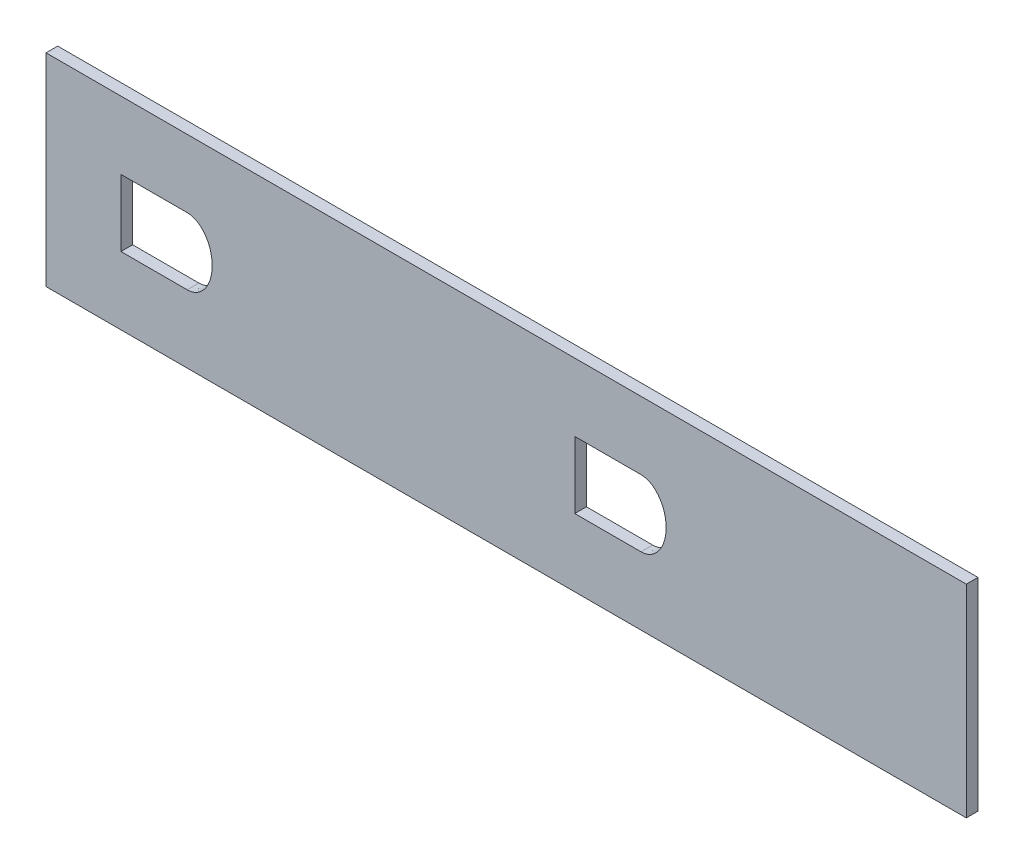
SolidWorks part; units mm, degrees
material "FiberBoard"
ref_plane "Front Plane" through (0, 0, 0) normal (0, 0, 1) x (1, 0, 0)
ref_plane "Top Plane" through (0, 0, 0) normal (0, 1, 0) x (1, 0, 0)
ref_plane "Right Plane" through (0, 0, 0) normal (1, 0, 0) x (0, 0, -1)
sketch "Sketch1" plane through (0, 0, 0) normal (0, 0, 1) x (1, 0, 0)
  line L0 (148.1213, 101.5831) -> (366.5883, 101.5831) construction
  line L1 (116.5883, 74.0831) -> (366.5883, 74.0831)
  line L2 (116.5883, 74.0831) -> (116.5883, 129.0831)
  line L3 (116.5883, 129.0831) -> (366.5883, 129.0831)
  line L4 (366.5883, 74.0831) -> (366.5883, 129.0831)
  line L5 (116.5883, 74.0831) -> (366.5883, 129.0831) construction
  line L6 (116.5883, 129.0831) -> (366.5883, 74.0831) construction
  line L7 (366.5883, -420.6524) -> (366.5883, 282.9047) construction
  line L8 (148.1213, 101.5831) -> (366.5883, 101.5831) construction
  line L9 (366.5883, -420.6524) -> (366.5883, 282.9047) construction
  line L10 (154.9444, 110.6594) -> (136.9445, 110.6594)
  line L11 (136.9445, 110.6594) -> (136.9445, 92.5118)
  line L12 (136.9445, 92.5118) -> (154.9445, 92.5118)
  line L13 (278.2224, 110.6594) -> (260.2224, 110.6594)
  line L14 (260.2224, 110.6594) -> (260.2224, 92.5118)
  line L15 (260.2224, 92.5118) -> (278.2227, 92.5118)
  spline S0 degree 3 poles (154.6577, 92.513) (155.4511, 92.5096) (155.9665, 92.5872) (156.7203, 92.818) (156.9673, 92.9142) (157.4406, 93.1371) (157.6687, 93.2643) (158.1094, 93.5479) (158.3228, 93.7053) (158.7258, 94.0399) (158.9164, 94.2176) (159.278, 94.5915) (159.449, 94.7878) (159.773, 95.1975) (159.9267, 95.4121) (160.3557, 96.0713) (160.5997, 96.5301) (161.0162, 97.4809) (161.189, 97.9743) (161.6026, 99.4931) (161.7336, 100.5249) (161.7356, 102.6231) (161.6059, 103.6537) (161.2008, 105.1594) (161.0282, 105.659) (160.6122, 106.6164) (160.3692, 107.0758) (159.8039, 107.9509) (159.478, 108.37) (158.7554, 109.1229) (158.3578, 109.4602) (157.4723, 110.0364) (157.0024, 110.2632) (156.2512, 110.4984) (155.9922, 110.5589) (155.4758, 110.6387) (155.2164, 110.6588) (154.695, 110.66) (154.4311, 110.6407) (153.9103, 110.5621) (153.6555, 110.5035) (152.9071, 110.2731) (152.4251, 110.0432) (151.7652, 109.6189) (151.5543, 109.4639) (151.1492, 109.1289) (150.9554, 108.9488) (150.4093, 108.3862) (150.0873, 107.9777) (149.6577, 107.3225) (149.523, 107.096) (149.2736, 106.6342) (149.1592, 106.3996) (148.8443, 105.6857) (148.6719, 105.1963) (148.3958, 104.1928) (148.2919, 103.6752) (148.1554, 102.6398) (148.1219, 102.1209) (148.1206, 101.0806) (148.1532, 100.5568) (148.288, 99.518) (148.3891, 99.0087) (148.6604, 98.0108) (148.8304, 97.5221) (149.247, 96.5677) (149.496, 96.0994) (150.0643, 95.2247) (150.3847, 94.814) (150.9306, 94.2462) (151.1238, 94.0652) (151.5254, 93.7296) (151.7347, 93.5739) (152.3905, 93.1466) (152.8717, 92.913) (153.6186, 92.6773) (153.8728, 92.6169) (154.3922, 92.5345) (154.6577, 92.513) (155.4511, 92.5096) (155.9665, 92.5872) knots -0.015625 -0.015625 0 0 0.03125 0.03125 0.046875 0.046875 0.0625 0.0625 0.078125 0.078125 0.09375 0.09375 0.109375 0.109375 0.125 0.125 0.15625 0.15625 0.1875 0.1875 0.25 0.25 0.3125 0.3125 0.34375 0.34375 0.375 0.375 0.40625 0.40625 0.4375 0.4375 0.46875 0.46875 0.484375 0.484375 0.5 0.5 0.515625 0.515625 0.53125 0.53125 0.5625 0.5625 0.578125 0.578125 0.59375 0.59375 0.625 0.625 0.640625 0.640625 0.65625 0.65625 0.6875 0.6875 0.71875 0.71875 0.75 0.75 0.78125 0.78125 0.8125 0.8125 0.84375 0.84375 0.875 0.875 0.90625 0.90625 0.921875 0.921875 0.9375 0.9375 0.96875 0.96875 0.984375 0.984375 1 1 1.03125 1.03125 1.046875 only from (154.9221, 92.5118) to (154.9221, 92.5118) construction
  spline S1 degree 3 poles (277.98, 92.5107) (278.7734, 92.5141) (279.2881, 92.5961) (280.04, 92.8322) (280.2866, 92.93) (280.7586, 93.1556) (280.9861, 93.2839) (281.4255, 93.5693) (281.6384, 93.7274) (282.0406, 94.0632) (282.2308, 94.2413) (282.5918, 94.6158) (282.7626, 94.8122) (283.0862, 95.222) (283.2395, 95.4363) (283.6689, 96.0961) (283.9131, 96.555) (284.3299, 97.5055) (284.5023, 97.9975) (284.9164, 99.518) (285.0464, 100.5497) (285.0448, 102.1218) (285.0106, 102.6441) (284.8751, 103.6719) (284.7738, 104.1795) (284.5681, 104.9309) (284.4905, 105.1797) (284.3162, 105.6737) (284.2194, 105.9187) (283.9034, 106.6357) (283.6579, 107.0939) (283.0882, 107.9655) (282.7602, 108.3827) (282.0335, 109.1325) (281.6346, 109.4678) (280.7484, 110.04) (280.2762, 110.2663) (279.5256, 110.4998) (279.2662, 110.56) (278.7491, 110.6392) (278.4896, 110.6591) (277.9686, 110.6598) (277.7057, 110.6404) (277.184, 110.561) (276.9291, 110.5019) (276.1813, 110.2701) (275.7, 110.039) (275.0414, 109.6121) (274.8312, 109.4563) (274.428, 109.1199) (274.2347, 108.9387) (273.6909, 108.3729) (273.3711, 107.9626) (272.8034, 107.0865) (272.5555, 106.6183) (272.1402, 105.6637) (271.9703, 105.1734) (271.6988, 104.1694) (271.597, 103.652) (271.4638, 102.6152) (271.4316, 102.096) (271.4324, 101.0561) (271.4655, 100.5345) (271.6014, 99.4936) (271.703, 98.9837) (271.9743, 97.9857) (272.1441, 97.4974) (272.5594, 96.545) (272.808, 96.0767) (273.3773, 95.2002) (273.698, 94.7897) (274.2439, 94.2236) (274.4377, 94.0426) (274.8409, 93.7075) (275.0509, 93.5524) (275.4893, 93.2694) (275.7176, 93.1414) (276.1948, 92.916) (276.4408, 92.8201) (276.9402, 92.6664) (277.1947, 92.6081) (277.7142, 92.5301) (277.98, 92.5107) (278.7734, 92.5141) (279.2881, 92.5961) knots -0.015625 -0.015625 0 0 0.03125 0.03125 0.046875 0.046875 0.0625 0.0625 0.078125 0.078125 0.09375 0.09375 0.109375 0.109375 0.125 0.125 0.15625 0.15625 0.1875 0.1875 0.25 0.25 0.28125 0.28125 0.3125 0.3125 0.328125 0.328125 0.34375 0.34375 0.375 0.375 0.40625 0.40625 0.4375 0.4375 0.46875 0.46875 0.484375 0.484375 0.5 0.5 0.515625 0.515625 0.53125 0.53125 0.5625 0.5625 0.578125 0.578125 0.59375 0.59375 0.625 0.625 0.65625 0.65625 0.6875 0.6875 0.71875 0.71875 0.75 0.75 0.78125 0.78125 0.8125 0.8125 0.84375 0.84375 0.875 0.875 0.90625 0.90625 0.921875 0.921875 0.9375 0.9375 0.953125 0.953125 0.96875 0.96875 0.984375 0.984375 1 1 1.03125 1.03125 1.046875 only from (278.2445, 92.5118) to (278.2445, 92.5118) construction
  spline S2 degree 3 poles (154.9445, 92.5118) (155.4656, 92.5118) (155.9736, 92.5894) (156.7203, 92.818) (156.9673, 92.9142) (157.4406, 93.1371) (157.6687, 93.2643) (158.1094, 93.5479) (158.3228, 93.7053) (158.7258, 94.0399) (158.9164, 94.2176) (159.278, 94.5915) (159.449, 94.7878) (159.773, 95.1975) (159.9267, 95.4121) (160.3557, 96.0713) (160.5997, 96.5301) (161.0162, 97.4809) (161.189, 97.9743) (161.6026, 99.4931) (161.7336, 100.5249) (161.7356, 102.6231) (161.6059, 103.6537) (161.2008, 105.1594) (161.0282, 105.659) (160.6122, 106.6164) (160.3692, 107.0758) (159.8039, 107.9509) (159.478, 108.37) (158.7554, 109.1229) (158.3578, 109.4602) (157.4723, 110.0364) (157.0024, 110.2632) (156.2512, 110.4984) (155.9922, 110.5589) (155.4758, 110.6387) (155.2164, 110.6588) (154.9519, 110.6594) (154.9482, 110.6594) (154.9444, 110.6594) knots 0.00044 0.00044 0.00044 0.00044 0.03125 0.03125 0.046875 0.046875 0.0625 0.0625 0.078125 0.078125 0.09375 0.09375 0.109375 0.109375 0.125 0.125 0.15625 0.15625 0.1875 0.1875 0.25 0.25 0.3125 0.3125 0.34375 0.34375 0.375 0.375 0.40625 0.40625 0.4375 0.4375 0.46875 0.46875 0.484375 0.484375 0.5 0.5 0.500225 0.500225 0.500225 0.500225
  spline S3 degree 3 poles (278.2227, 92.5118) (278.2299, 92.5118) (278.2372, 92.5118) (278.7734, 92.5141) (279.2881, 92.5961) (280.04, 92.8322) (280.2866, 92.93) (280.7586, 93.1556) (280.9861, 93.2839) (281.4255, 93.5693) (281.6384, 93.7274) (282.0406, 94.0632) (282.2308, 94.2413) (282.5918, 94.6158) (282.7626, 94.8122) (283.0862, 95.222) (283.2395, 95.4363) (283.6689, 96.0961) (283.9131, 96.555) (284.3299, 97.5055) (284.5023, 97.9975) (284.9164, 99.518) (285.0464, 100.5497) (285.0448, 102.1218) (285.0106, 102.6441) (284.8751, 103.6719) (284.7738, 104.1795) (284.5681, 104.9309) (284.4905, 105.1797) (284.3162, 105.6737) (284.2194, 105.9187) (283.9034, 106.6357) (283.6579, 107.0939) (283.0882, 107.9655) (282.7602, 108.3827) (282.0335, 109.1325) (281.6346, 109.4678) (280.7484, 110.04) (280.2762, 110.2663) (279.5256, 110.4998) (279.2662, 110.56) (278.7491, 110.6392) (278.4896, 110.6591) (278.2268, 110.6594) (278.2246, 110.6594) (278.2224, 110.6594) knots 0.999571 0.999571 0.999571 0.999571 1 1 1.03125 1.03125 1.046875 1.046875 1.0625 1.0625 1.078125 1.078125 1.09375 1.09375 1.109375 1.109375 1.125 1.125 1.15625 1.15625 1.1875 1.1875 1.25 1.25 1.28125 1.28125 1.3125 1.3125 1.328125 1.328125 1.34375 1.34375 1.375 1.375 1.40625 1.40625 1.4375 1.4375 1.46875 1.46875 1.484375 1.484375 1.5 1.5 1.500135 1.500135 1.500135 1.500135
  point P0 (241.5883, 101.5831)
  point P11 (366.5883, 101.5831)
  point P19 (278.0934, 110.6578)
  dimension "D1" = 250
  dimension "D2" = 55
  dimension "D3" = 18
  dimension "D4" = 18
  dimension "D5" = 18
extrude "Boss-Extrude1" add sketch "Sketch1" along normal blind 3.175
